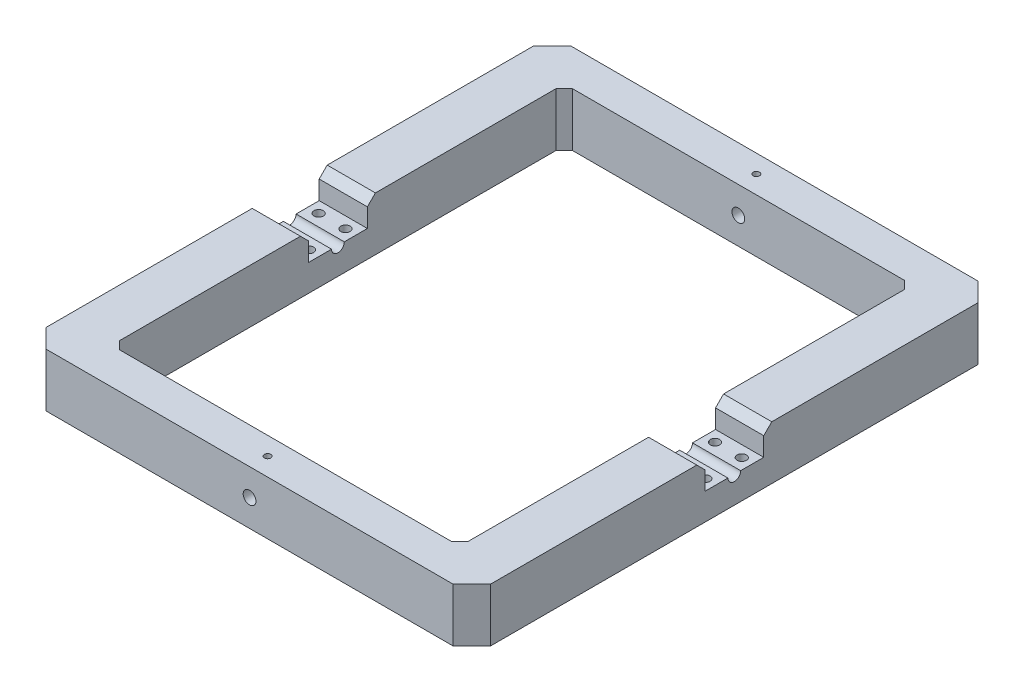
SolidWorks part; units mm, degrees
ref_plane "Front Plane" through (0, 0, 0) normal (0, 0, 1) x (1, 0, 0)
ref_plane "Top Plane" through (0, 0, 0) normal (0, 1, 0) x (1, 0, 0)
ref_plane "Right Plane" through (0, 0, 0) normal (1, 0, 0) x (0, 0, -1)
sketch "Sketch1" plane through (0, 0, 0) normal (0, 1, 0) x (1, 0, 0)
  line L0 (-83, 98) -> (-83, -98)
  line L1 (-65, 80) -> (65, 80)
  line L2 (-65, 80) -> (-65, -80)
  line L3 (-65, -80) -> (65, -80)
  line L4 (65, 80) -> (65, -80)
  line L5 (-65, 80) -> (65, -80) construction
  line L6 (-65, -80) -> (65, 80) construction
  line L7 (-83, -98) -> (83, -98)
  line L8 (83, 98) -> (83, -98)
  line L9 (-83, 98) -> (83, 98)
  point P0 (0, 0)
  dimension "D2" = 130
  dimension "D3" = 160
  dimension "D1" = 18
extrude "Boss-Extrude1" add sketch "Sketch1" along normal mid plane 20
sketch "Sketch2" plane through (83, 0, 0) normal (1, 0, 0) x (0, 0, -1)
  circle A0 centre (0, 0) radius 2.3813
  dimension "D1" = 4.7625
extrude "Cut-Extrude1" cut sketch "Sketch2" against normal up to next
sketch "Sketch3" plane through (-83, 0, 0) normal (-1, 0, 0) x (0, 0, 1)
  line L0 (-98, 0) -> (98, 0) construction
  line L1 (-98, 10) -> (-98, -10) construction
  line L2 (98, 10) -> (98, -10) construction
  line L3 (-98, 10) -> (98, 10) construction
  line L4 (-11, 0) -> (11, 0)
  line L5 (-11, 0) -> (-11, 10)
  line L6 (-11, 10) -> (11, 10)
  line L7 (11, 0) -> (11, 10)
  circle A0 centre (0, 0) radius 2.3813
  point P12 (0, 0)
  line M7 (98, 10) -> (-98, 10)
  dimension "D2" = 4.7625
  dimension "D1" = 22
extrude "Cut-Extrude2" cut sketch "Sketch3" against normal through all contours A0 L4 L7 L5 M7 | L4 A0 | L4 A0
sketch "Sketch5" plane through (0, 0, 98) normal (0, 0, 1) x (1, 0, 0)
  line L0 (-83, 0) -> (83, 0) construction
  line L1 (83, 10) -> (83, -10) construction
  circle A0 centre (0, 0) radius 2.3813
  dimension "D1" = 4.7625
extrude "Cut-Extrude4" cut sketch "Sketch5" against normal through all both and the other way through all
sketch "Sketch6" plane through (0, 0, 0) normal (0, 1, 0) x (1, 0, 0)
  line L0 (0, 80) -> (0, -80) construction
  line L1 (65, 80) -> (-65, 80) construction
  line L2 (-65, -80) -> (65, -80) construction
  line L3 (-74, 11) -> (-74, -11) construction
  line L4 (-65, 11) -> (-83, 11) construction
  line L5 (-65, -11) -> (-83, -11) construction
  line L6 (-83, 0) -> (-65, 0) construction
  line L9 (-83, 2.3812) -> (-83, -2.3813) construction
  line L10 (-65, -2.3813) -> (-65, 2.3812) construction
  line L11 (-69, 6.8) -> (-69, -6.8) construction
  circle A0 centre (-69, 6.8) radius 1.75
  circle A1 centre (-69, -6.8) radius 1.75
  circle A2 centre (-79, -6.8) radius 1.75
  circle A3 centre (-79, 6.8) radius 1.75
  circle A4 centre (79, 6.8) radius 1.75
  circle A5 centre (79, -6.8) radius 1.75
  circle A6 centre (69, -6.8) radius 1.75
  circle A7 centre (69, 6.8) radius 1.75
  point P20 (-69, 0)
  dimension "D1" = 3.5
  dimension "D2" = 3.5
  dimension "D3" = 5
  dimension "D4" = 6.8
extrude "Cut-Extrude5" cut sketch "Sketch6" against normal up to next
sketch "Sketch8" plane through (0, 10, 0) normal (0, 1, 0) x (1, 0, 0)
  line L0 (65, 11) -> (65, 80) construction
  line L1 (-65, 80) -> (65, 80)
  line L2 (-65, 80) -> (-65, 84.5)
  line L3 (-65, 84.5) -> (65, 84.5)
  line L4 (65, 80) -> (65, 84.5)
  line L10 (-65, 0) -> (65, 0) construction
  line L11 (-65, -2.3813) -> (-65, 2.3812) construction
  line L12 (65, 2.3813) -> (65, -2.3812) construction
  line L13 (-65, -84.5) -> (65, -84.5)
  line L14 (65, -80) -> (65, -84.5)
  line L15 (-65, -80) -> (65, -80)
  line L16 (-65, -80) -> (-65, -84.5)
  dimension "D1" = 4.5
extrude "Cut-Extrude7" cut sketch "Sketch8" against normal up to next
chamfer "Chamfer9" distance 7 angle 45 4 edges at (-83, 0, -98) (83, 0, -98) (83, 0, 98) (-83, 0, 98)
chamfer "Chamfer10" distance 3 angle 45 4 edges at (65, 0, -84.5) (-65, 0, -84.5) (-65, 0, 84.5) (65, 0, 84.5)
sketch "Sketch9" plane through (0, 10, 0) normal (0, 1, 0) x (1, 0, 0)
  line L0 (-65, 0) -> (65, 0) construction
  line L1 (-65, -2.3813) -> (-65, 2.3812) construction
  line L2 (65, 2.3813) -> (65, -2.3812) construction
  line L3 (0, 84.5) -> (0, 98) construction
  line L4 (62, 84.5) -> (-62, 84.5) construction
  line L5 (76, 98) -> (-76, 98) construction
  circle A0 centre (0, 91.25) radius 1.1906
  circle A1 centre (0, -91.25) radius 1.1906
  dimension "D1" = 2.3813
extrude "Cut-Extrude8" cut sketch "Sketch9" against normal up to next
chamfer "Chamfer11" distance 3 angle 45 4 edges at (74, 10, 11) (74, 10, -11) (-74, 10, 11) (-74, 10, -11)
